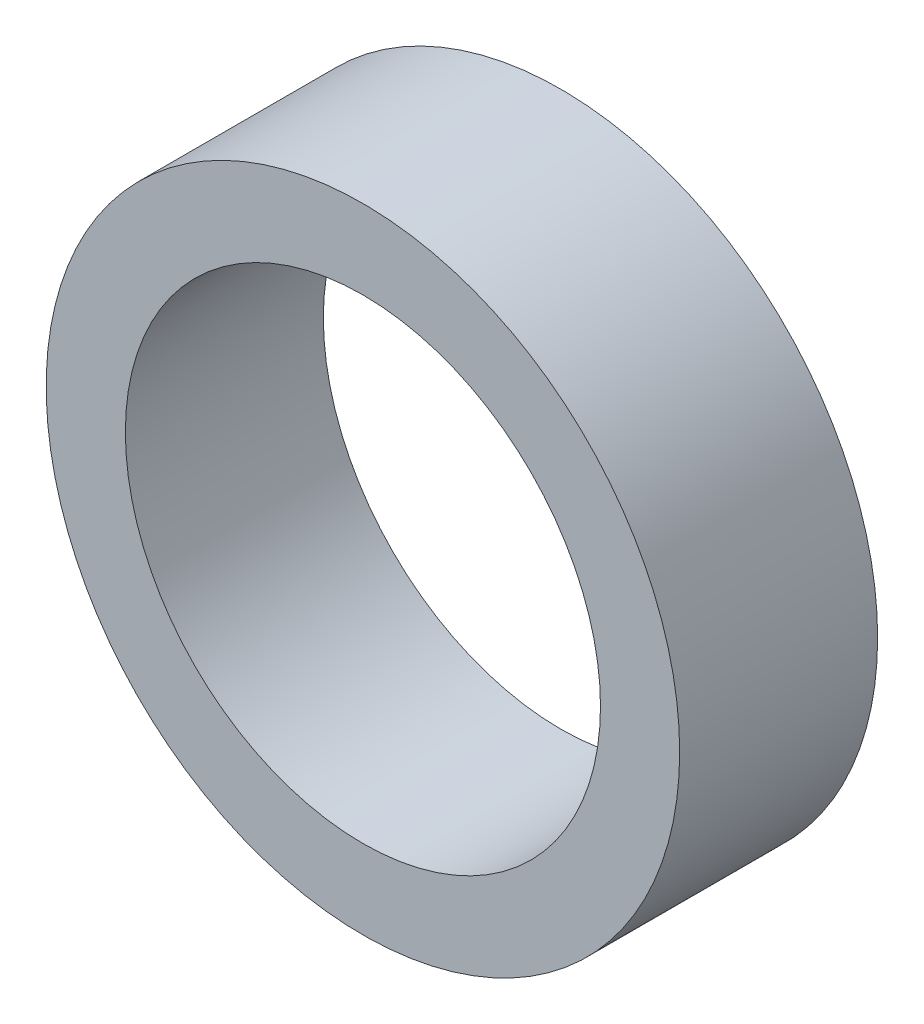
SolidWorks part; units mm, degrees
ref_plane "Alzado" through (0, 0, 0) normal (0, 0, 1) x (1, 0, 0)
ref_plane "Planta" through (0, 0, 0) normal (0, 1, 0) x (1, 0, 0)
ref_plane "Vista lateral" through (0, 0, 0) normal (1, 0, 0) x (0, 0, -1)
sketch "Croquis3" plane through (0, 0, 0) normal (0, 0, 1) x (1, 0, 0)
  circle A0 centre (0, 0) radius 16
  circle A1 centre (0, 0) radius 12
extrude "Saliente-Extruir2" add sketch "Croquis3" along normal blind 10 contours A0
sketch "Croquis4" plane through (0, 0, 10) normal (0, 0, 1) x (1, 0, 0)
  circle A0 centre (0, 0) radius 12
extrude "Cortar-Extruir1" cut sketch "Croquis4" against normal blind 10
scale "Escala1" scale about centroid uniform scaling yes scale factor 7
